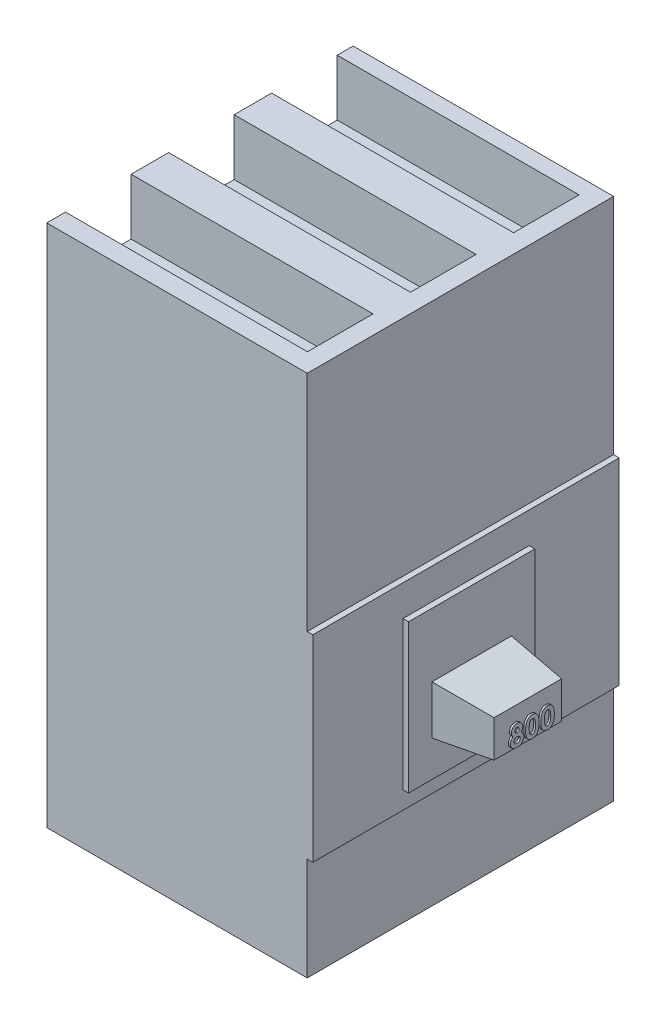
SolidWorks part; units mm, degrees
ref_plane "Alzado" through (0, 0, 0) normal (0, 0, 1) x (1, 0, 0)
ref_plane "Planta" through (0, 0, 0) normal (0, 1, 0) x (1, 0, 0)
ref_plane "Vista lateral" through (0, 0, 0) normal (1, 0, 0) x (0, 0, -1)
sketch "Croquis1" plane through (0, 0, 0) normal (0, 0, 1) x (1, 0, 0)
  line L1 (-69.5, -139.75) -> (69.5, -139.75)
  line L2 (-69.5, -139.75) -> (-69.5, 139.75)
  line L3 (-69.5, 139.75) -> (69.5, 139.75)
  line L4 (69.5, -139.75) -> (69.5, 139.75)
  line L5 (-69.5, -139.75) -> (69.5, 139.75) construction
  line L6 (-69.5, 139.75) -> (69.5, -139.75) construction
  point P0 (0, 0)
  dimension "D1" = 279.5
  dimension "D2" = 139
extrude "Saliente-Extruir1" add sketch "Croquis1" along normal blind 163.5
sketch "Croquis2" plane through (69.5, 0, 0) normal (1, 0, 0) x (0, 0, -1)
  line L0 (0, -139.75) -> (0, 139.75) construction
  line L1 (-163.5, -84.7658) -> (0, -84.7658)
  line L2 (-163.5, -84.7658) -> (-163.5, 20.3792)
  line L3 (-163.5, 20.3792) -> (0, 20.3792)
  line L4 (0, -84.7658) -> (0, 20.3792)
  line L5 (-163.5, -84.7658) -> (0, 20.3792) construction
  line L6 (-163.5, 20.3792) -> (0, -84.7658) construction
  point P0 (-81.75, -32.1933)
extrude "Saliente-Extruir2" add sketch "Croquis2" along normal blind 3
sketch "Croquis3" plane through (72.5, 0, 0) normal (1, 0, 0) x (0, 0, -1)
  line L1 (-115.42, -75.3146) -> (-48.08, -75.3146)
  line L2 (-115.42, -75.3146) -> (-115.42, 3.8396)
  line L3 (-115.42, 3.8396) -> (-48.08, 3.8396)
  line L4 (-48.08, -75.3146) -> (-48.08, 3.8396)
  line L5 (-115.42, -75.3146) -> (-48.08, 3.8396) construction
  line L6 (-115.42, 3.8396) -> (-48.08, -75.3146) construction
  point P0 (-81.75, -35.7375)
extrude "Saliente-Extruir3" add sketch "Croquis3" along normal blind 3
sketch "Croquis4" plane through (75.5, 0, 0) normal (1, 0, 0) x (0, 0, -1)
  line L1 (-102.9404, -56.0749) -> (-60.5596, -56.0749)
  line L2 (-102.9404, -56.0749) -> (-102.9404, -30.1544)
  line L3 (-102.9404, -30.1544) -> (-60.5596, -30.1544)
  line L4 (-60.5596, -56.0749) -> (-60.5596, -30.1544)
  line L5 (-102.9404, -56.0749) -> (-60.5596, -30.1544) construction
  line L6 (-102.9404, -30.1544) -> (-60.5596, -56.0749) construction
  point P0 (-81.75, -52.2772)
  point P1 (-81.75, -43.1146)
extrude "Saliente-Extruir4" add sketch "Croquis4" along normal blind 30 draft 6
sketch "Croquis6" plane through (0, 139.75, 0) normal (0, 1, 0) x (1, 0, 0)
  line L0 (59.6081, -153.5) -> (-69.5, -153.5)
  line L1 (-69.5, -163.5) -> (-69.5, 0) construction
  line L2 (-69.5, -153.5) -> (-69.5, -118.5)
  line L3 (-69.5, -118.5) -> (59.6081, -118.5)
  line L4 (59.6081, -118.5) -> (59.6081, -153.5)
  line L5 (59.6081, -98.5) -> (-69.5, -98.5)
  line L6 (-69.5, -98.5) -> (-69.5, -63.5)
  line L7 (-69.5, -63.5) -> (59.6081, -63.5)
  line L8 (59.6081, -63.5) -> (59.6081, -98.5)
  line L9 (59.6081, -43.5) -> (-69.5, -43.5)
  line L10 (-69.5, -43.5) -> (-69.5, -8.5)
  line L11 (-69.5, -8.5) -> (59.6081, -8.5)
  line L12 (59.6081, -8.5) -> (59.6081, -43.5)
  line L13 (69.5, -163.5) -> (-69.5, -163.5) construction
  dimension "D1" = 35
  dimension "D2" = 35
  dimension "D3" = 10
  dimension "D4" = 20
  dimension "D5" = 20
  dimension "D6" = 35
extrude "Cortar-Extruir1" cut sketch "Croquis6" against normal blind 30
sketch "Croquis7" plane through (0, 109.75, 0) normal (0, 1, 0) x (1, 0, 0)
  circle A0 centre (-40.6211, -136) radius 8
  circle A1 centre (-40.6211, -81) radius 8
  circle A2 centre (-40.6211, -26) radius 8
  dimension "D1" = 16
  dimension "D2" = 16
  dimension "D3" = 16
extrude "Cortar-Extruir2" cut sketch "Croquis7" against normal blind 30
sketch "Croquis8" plane through (105.5, 0, 0) normal (1, 0, 0) x (0, 0, -1)
  line L0 (-96.5835, -51.8971) -> (-66.3339, -51.8971) construction
  text T0 " 800" font "Century Gothic" height in points 40
extrude "Saliente-Extruir5" add sketch "Croquis8" along normal blind 1
